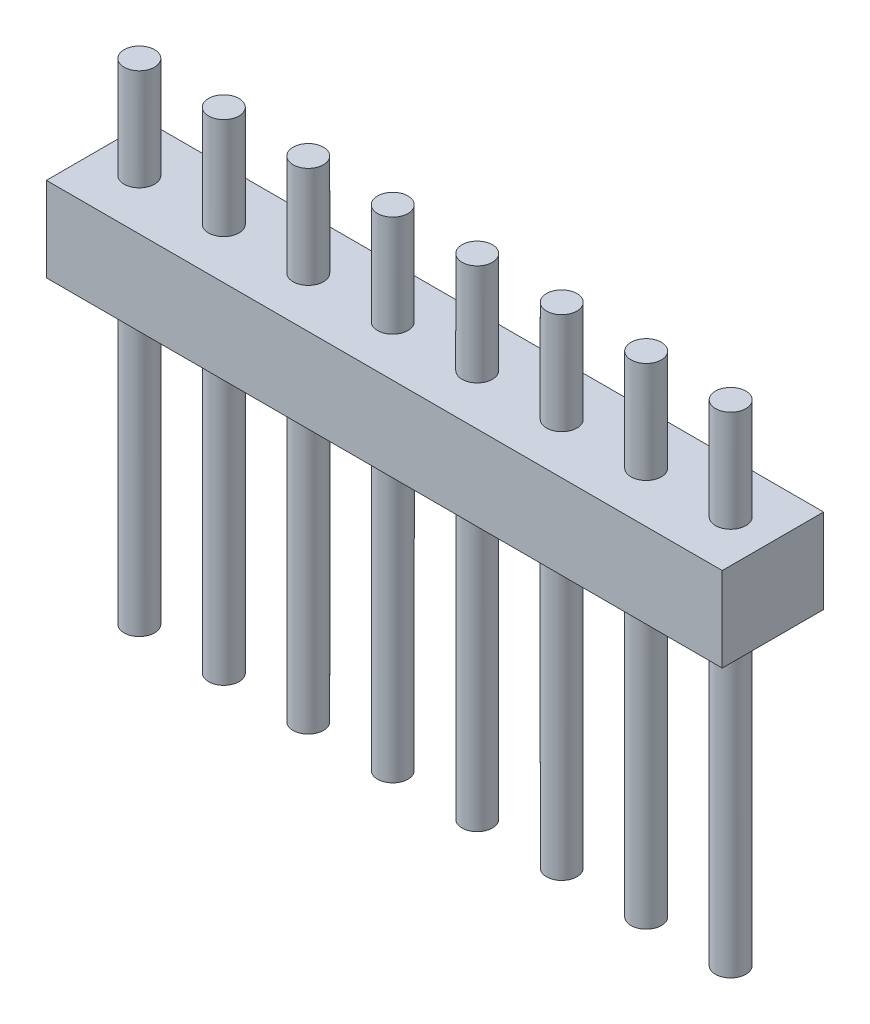
SolidWorks part; units mm, degrees
ref_plane "Alzado" through (0, 0, 0) normal (0, 0, 1) x (1, 0, 0)
ref_plane "Planta" through (0, 0, 0) normal (0, 1, 0) x (1, 0, 0)
ref_plane "Vista lateral" through (0, 0, 0) normal (1, 0, 0) x (0, 0, -1)
sketch "Croquis1" plane through (0, 0, 0) normal (0, 0, 1) x (1, 0, 0)
  line L1 (-10, 1.25) -> (10, 1.25)
  line L2 (-10, 1.25) -> (-10, -1.25)
  line L3 (-10, -1.25) -> (10, -1.25)
  line L4 (10, 1.25) -> (10, -1.25)
  line L5 (-10, 1.25) -> (10, -1.25) construction
  line L6 (-10, -1.25) -> (10, 1.25) construction
  point P0 (0, 0)
  dimension "D1" = 2.5
  dimension "D2" = 20
extrude "Saliente-Extruir1" add sketch "Croquis1" along normal blind 3
sketch "Croquis2" plane through (0, 1.25, 0) normal (0, 1, 0) x (1, 0, 0)
  line L0 (-10, -1.5) -> (-8.75, -1.5) construction
  line L1 (-10, -3) -> (-10, 0) construction
  circle A0 centre (-8.75, -1.5) radius 0.45
  circle A1 centre (-6.25, -1.5) radius 0.45
  circle A2 centre (-3.75, -1.5) radius 0.45
  circle A3 centre (-1.25, -1.5) radius 0.45
  circle A4 centre (1.25, -1.5) radius 0.45
  circle A5 centre (3.75, -1.5) radius 0.45
  circle A6 centre (6.25, -1.5) radius 0.45
  circle A7 centre (8.75, -1.5) radius 0.45
  dimension "D1" = 0.9
  dimension "D2" = 1.25
  dimension "D3" = 8
extrude "Saliente-Extruir2" add sketch "Croquis2" along normal blind 3
sketch "Croquis3" plane through (0, -1.25, 0) normal (0, -1, 0) x (1, 0, 0)
  line L0 (-10, 1.5) -> (-8.75, 1.5) construction
  line L1 (-10, 3) -> (-10, 0) construction
  circle A0 centre (-8.75, 1.5) radius 0.45
  circle A1 centre (-6.25, 1.5) radius 0.45
  circle A2 centre (-3.75, 1.5) radius 0.45
  circle A3 centre (-1.25, 1.5) radius 0.45
  circle A4 centre (1.25, 1.5) radius 0.45
  circle A5 centre (3.75, 1.5) radius 0.45
  circle A6 centre (6.25, 1.5) radius 0.45
  circle A7 centre (8.75, 1.5) radius 0.45
  dimension "D1" = 8
extrude "Saliente-Extruir3" add sketch "Croquis3" along normal blind 9
